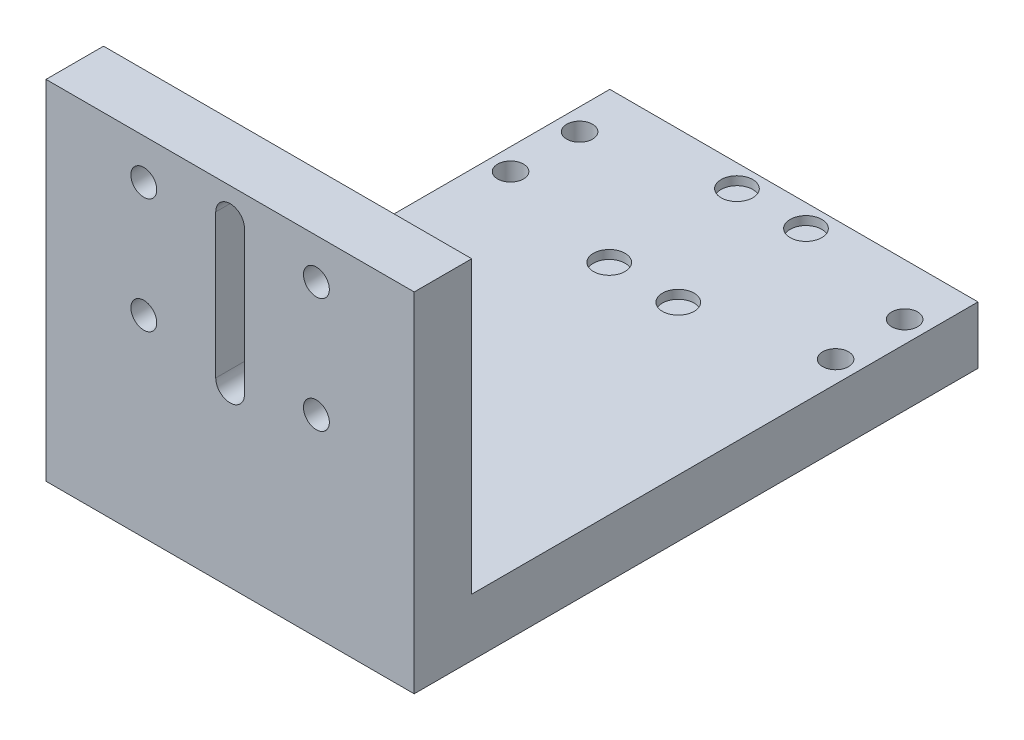
SolidWorks part; units mm, degrees
ref_plane "Front Plane" through (0, 0, 0) normal (0, 0, 1) x (1, 0, 0)
ref_plane "Top Plane" through (0, 0, 0) normal (0, 1, 0) x (1, 0, 0)
ref_plane "Right Plane" through (0, 0, 0) normal (1, 0, 0) x (0, 0, -1)
sketch "Sketch1" plane through (0, 0, 0) normal (1, 0, 0) x (0, 0, -1)
  line L0 (0, 60.5) -> (0, 0)
  line L1 (0, 0) -> (98, 0)
  line L2 (98, 0) -> (98, 10)
  line L3 (98, 10) -> (10, 10)
  line L4 (10, 10) -> (10, 60.5)
  line L5 (10, 60.5) -> (0, 60.5)
  dimension "D1" = 98
  dimension "D2" = 10
  dimension "D3" = 10
  dimension "D4" = 60.5
extrude "Boss-Extrude1" add sketch "Sketch1" along normal blind 64
ref_plane "Plane1" through (32, 0, 0) normal (-1, 0, 0) x (0, 0, 1)
sketch "Sketch3" plane through (0, 0, -10) normal (0, 0, -1) x (-1, 0, 0)
  line L0 (-64, 60.5) -> (0, 60.5) construction
  line L1 (-32, -4.4) -> (-32, 4.4) construction
  circle A0 centre (-47, 53.5) radius 2.25
  dimension "D1" = 7
  dimension "D3" = 4.5
  dimension "D2" = 15
extrude "Cut-Extrude1" cut sketch "Sketch3" against normal up to next (10 mm away)
pattern_linear "LPattern1" count 2 spacing 30 along (-1, 0, 0) count 2 spacing 20 along (0, -1, 0) of "Cut-Extrude1"
sketch "Sketch4" plane through (0, 10, 0) normal (0, 1, 0) x (1, 0, 0)
  line L0 (64, 98) -> (0, 98) construction
  line L1 (64, 98) -> (64, 10) construction
  circle A0 centre (60.25, 89) radius 2.25
  dimension "D1" = 4.5
  dimension "D2" = 9
  dimension "D3" = 3.75
extrude "Cut-Extrude2" cut sketch "Sketch4" against normal up to next (10 mm away)
pattern_linear "LPattern2" count 2 spacing 12 along (0, 0, 1) count 2 spacing 56.5 along (-1, 0, 0) of "Cut-Extrude2"
sketch "Sketch5" plane through (0, 0, -10) normal (0, 0, -1) x (-1, 0, 0)
  line L0 (-32, 55.3) -> (-32, 30.3) construction
  line L1 (-32, -4.4) -> (-32, 4.4) construction
  line L2 (-29.5, 55.3) -> (-29.5, 30.3)
  line L3 (-34.5, 55.3) -> (-34.5, 30.3)
  line L4 (-64, 60.5) -> (0, 60.5) construction
  arc A0 (-29.5, 55.3) -> (-34.5, 55.3) centre (-32, 55.3) ccw
  arc A1 (-34.5, 30.3) -> (-29.5, 30.3) centre (-32, 30.3) ccw
  point P4 (-32, 42.8)
  dimension "D2" = 2.5
  dimension "D3" = 25
  dimension "D1" = 5.2
extrude "Cut-Extrude3" cut sketch "Sketch5" against normal blind 10
sketch "Sketch6" plane through (0, 10, 0) normal (0, 1, 0) x (1, 0, 0)
  line L0 (64, 98) -> (0, 98) construction
  line L1 (64, 98) -> (64, 10) construction
  circle A0 centre (38, 94.1) radius 2.75
  dimension "D1" = 5.5
  dimension "D2" = 3.9
  dimension "D3" = 26
extrude "Cut-Extrude4" cut sketch "Sketch6" against normal blind 1.5
pattern_linear "LPattern3" count 2 spacing 12 along (-1, 0, 0) count 2 spacing 22.2 along (0, 0, 1) of "Cut-Extrude4"
chamfer "Chamfer1" [suppressed] distance 0.5 angle 45
